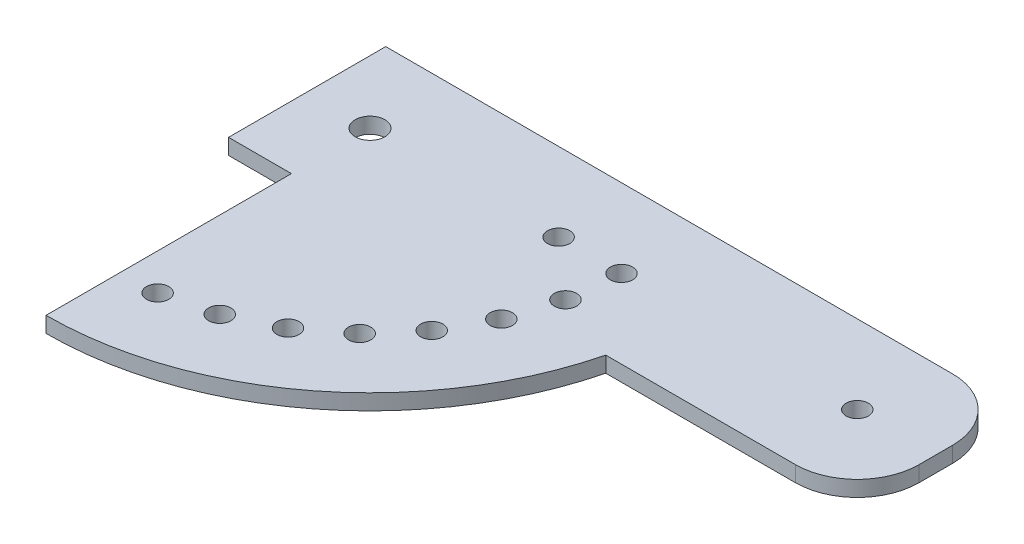
SolidWorks part; units mm, degrees
ref_plane "Front Plane" through (0, 0, 0) normal (0, 0, 1) x (1, 0, 0)
ref_plane "Top Plane" through (0, 0, 0) normal (0, 1, 0) x (1, 0, 0)
ref_plane "Right Plane" through (0, 0, 0) normal (1, 0, 0) x (0, 0, -1)
sketch "Sketch1" plane through (0, 0, 0) normal (0, 1, 0) x (1, 0, 0)
  line L0 (-12.7, -15.875) -> (-12.7, 15.875)
  line L1 (-12.7, 15.875) -> (101.8, 15.875)
  line L2 (114.3, 3.375) -> (114.3, -3.375)
  line L3 (101.8, -15.875) -> (63.5, -15.875)
  line L4 (-12.7, -15.875) -> (0, -15.875)
  line L5 (0, 0) -> (50.8, 0) construction
  line L6 (0, -65.4543) -> (0, -15.875)
  line L7 (0, 0) -> (50.8, 0) construction
  line L8 (0, 0) -> (49.7505, -10.2727) construction
  circle A0 centre (0, 0) radius 3
  circle A2 centre (98.425, 0) radius 2.25
  arc A4 (63.5, -15.875) -> (0, -65.4543) centre (0, 0) cw
  circle A5 centre (50.8, 0) radius 2.25
  circle A6 centre (49.7505, -10.2727) radius 2.25
  circle A7 centre (46.6454, -20.1209) radius 2.25
  circle A8 centre (41.6129, -29.1378) radius 2.25
  circle A9 centre (34.861, -36.9507) radius 2.25
  circle A10 centre (26.6687, -43.2368) radius 2.25
  circle A11 centre (17.3745, -47.7364) radius 2.25
  circle A12 centre (7.3623, -50.2637) radius 2.25
  arc A13 (114.3, -3.375) -> (101.8, -15.875) centre (101.8, -3.375) cw
  arc A14 (101.8, 15.875) -> (114.3, 3.375) centre (101.8, 3.375) cw
  circle A15 centre (38.1, 0) radius 2.25
  point P2 (-12.7, 0)
  dimension "D4" = 6
  dimension "D5" = 4.5
  dimension "D10" = 4.5
  dimension "D9" = 12.5
  dimension "D1" = 31.75
  dimension "D2" = 12.7
  dimension "D3" = 114.3
  dimension "D6" = 15.875
  dimension "D7" = 50.8
  dimension "D8" = 12.7
  dimension "D12" = 11.667
  dimension "D13" = 38.1
  dimension "D11" = 8
extrude "Boss-Extrude1" add sketch "Sketch1" along normal blind 3.175
